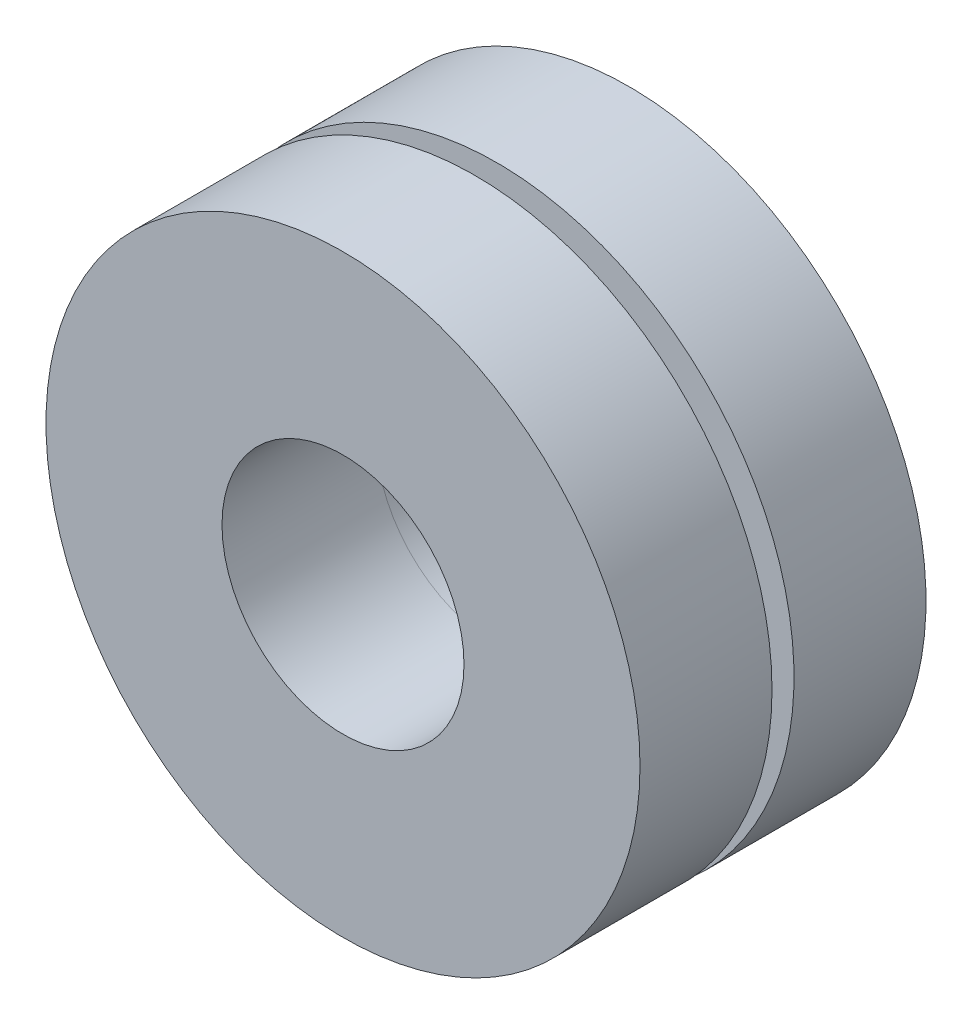
SolidWorks part; units mm, degrees
ref_plane "Front Plane" through (0, 0, 0) normal (0, 0, 1) x (1, 0, 0)
ref_plane "Top Plane" through (0, 0, 0) normal (0, 1, 0) x (1, 0, 0)
ref_plane "Right Plane" through (0, 0, 0) normal (1, 0, 0) x (0, 0, -1)
sketch "Sketch1" plane through (0, 0, 0) normal (0, 0, 1) x (1, 0, 0)
  circle A0 centre (0, 0) radius 2.794
  circle A1 centre (0, 0) radius 6.096
  dimension "D1" = 3.302
  dimension "D2" = 5.588
extrude "Boss-Extrude2" add sketch "Sketch1" along normal blind 0.508 contours A1
sketch "Sketch3" plane through (0, 0, 0.508) normal (0, 0, 1) x (1, 0, 0)
  circle A0 centre (0, 0) radius 2.794
  circle A1 centre (0, 0) radius 6.858
  dimension "D1" = 4.064
  dimension "D2" = 5.588
extrude "Boss-Extrude3" add sketch "Sketch3" along normal blind 3.048
sketch "Sketch4" plane through (0, 0, 0) normal (0, 0, -1) x (-1, 0, 0)
  circle A0 centre (0, 0) radius 2.794
  circle A1 centre (0, 0) radius 6.858
  dimension "D1" = 5.588
extrude "Boss-Extrude4" add sketch "Sketch4" along normal blind 3.048 separate body
